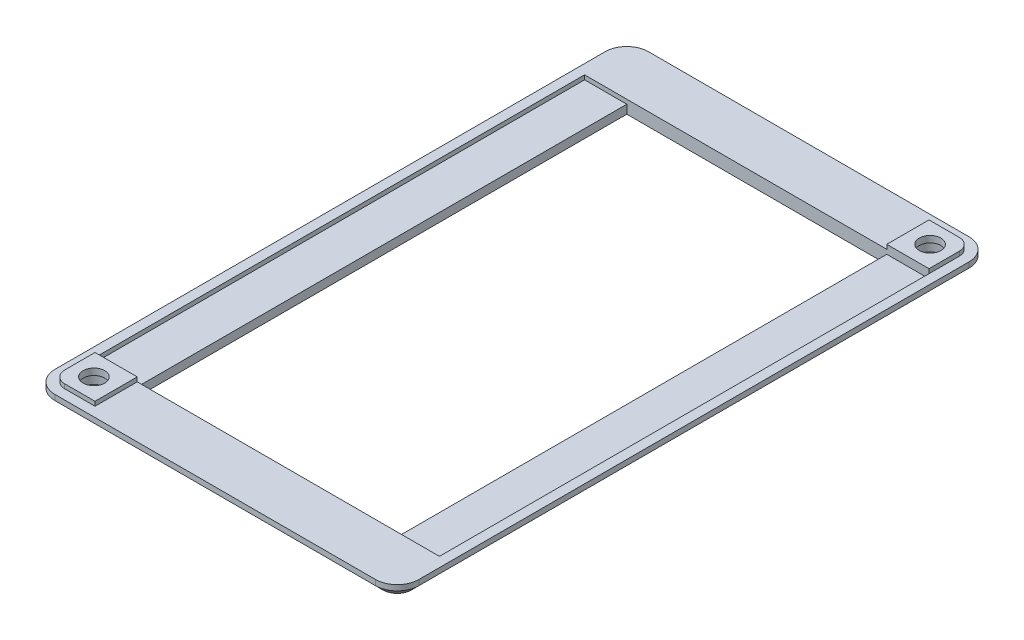
SolidWorks part; units mm, degrees
ref_plane "Front Plane" through (0, 0, 0) normal (0, 0, 1) x (1, 0, 0)
ref_plane "Top Plane" through (0, 0, 0) normal (0, 1, 0) x (1, 0, 0)
ref_plane "Right Plane" through (0, 0, 0) normal (1, 0, 0) x (0, 0, -1)
sketch "Sketch1" plane through (0, 0, 0) normal (0, 1, 0) x (1, 0, 0)
  line L1 (0, 0) -> (84, 0)
  line L2 (0, 0) -> (0, 137)
  line L3 (0, 137) -> (84, 137)
  line L4 (84, 0) -> (84, 137)
  dimension "D1" = 84
  dimension "D2" = 137
extrude "Boss-Extrude1" add sketch "Sketch1" along normal blind 3
sketch "Sketch3" plane through (0, 3, 0) normal (0, 1, 0) x (1, 0, 0)
  line L0 (81.75, 125) -> (72, 125)
  line L1 (72, 125) -> (72, 134.75)
  line L4 (12, 2.25) -> (12, 12)
  line L5 (12, 12) -> (2.25, 12)
  line L8 (2.25, 134.75) -> (2.25, 2.25)
  line L9 (2.25, 2.25) -> (81.75, 2.25)
  line L10 (81.75, 2.25) -> (81.75, 134.75)
  line L11 (81.75, 134.75) -> (2.25, 134.75)
  line L12 (2.25, 12) -> (2.25, 5)
  line L13 (5, 2.25) -> (12, 2.25)
  line L14 (81.75, 125) -> (81.75, 132)
  line L15 (79, 134.75) -> (72, 134.75)
  line L16 (0, 137) -> (0, 0)
  line L17 (0, 0) -> (84, 0)
  line L18 (84, 0) -> (84, 137)
  line L19 (84, 137) -> (0, 137)
  line L20 (0, 137) -> (0, 0) construction
  line L21 (0, 0) -> (84, 0) construction
  line L22 (84, 0) -> (84, 137) construction
  line L23 (84, 137) -> (0, 137) construction
  arc A0 (81.75, 132) -> (79, 134.75) centre (79, 132) ccw
  arc A1 (2.25, 5) -> (5, 2.25) centre (5, 5) ccw
  dimension "D2" = 2.75
  dimension "D4" = 12
  dimension "D5" = 12
  dimension "D6" = 12
  dimension "D7" = 12
  dimension "D1" = 2.25
  dimension "D3" = 0
extrude "Boss-Extrude2" add sketch "Sketch3" along normal blind 1
fillet "Fillet1" radius 5 4 edges at (84, 1.5, 0) (0, 1.5, 0) (0, 1.5, -137) (84, 1.5, -137)
sketch "Sketch4" plane through (0, 4, 0) normal (0, 1, 0) x (1, 0, 0)
  line L0 (72, 125) -> (81.75, 125) construction
  line L1 (72, 134.75) -> (72, 125) construction
  line L2 (12, 12) -> (2.25, 12) construction
  line L3 (12, 2.25) -> (12, 12) construction
  line L4 (72, 125) -> (81.75, 125) construction
  line L5 (72, 134.75) -> (72, 125) construction
  line L6 (12, 12) -> (2.25, 12) construction
  line L7 (12, 2.25) -> (12, 12) construction
  circle A0 centre (7, 7) radius 2.5
  circle A1 centre (77, 130) radius 2.5
  dimension "D1" = 5
  dimension "D4" = 5
  dimension "D2" = 5
  dimension "D3" = 5
  dimension "D5" = 5
  dimension "D6" = 5
extrude "Cut-Extrude1" cut sketch "Sketch4" against normal through all
ref_plane "Plane4" through (0, 2.5, 0) normal (0, 1, 0) x (1, 0, 0)
sketch "Sketch5" plane through (0, 2.5, 0) normal (0, 1, 0) x (1, 0, 0)
  circle A0 centre (77, 130) radius 2.5 construction
  circle A1 centre (7, 7) radius 2.5 construction
  circle A2 centre (77, 130) radius 2.5 construction
  circle A3 centre (7, 7) radius 2.5 construction
  circle A4 centre (7, 7) radius 3.5
  circle A5 centre (77, 130) radius 3.5
  dimension "D1" = 7
  dimension "D2" = 7
extrude "Cut-Extrude2" cut sketch "Sketch5" against normal through all
sketch "Sketch6" plane through (0, 3, 0) normal (0, 1, 0) x (1, 0, 0)
  line L1 (12, 12) -> (72, 12)
  line L2 (12, 12) -> (12, 125)
  line L3 (12, 125) -> (72, 125)
  line L4 (72, 12) -> (72, 125)
extrude "Cut-Extrude3" cut sketch "Sketch6" against normal through all
sketch "Sketch7" plane through (0, 3, 0) normal (0, 1, 0) x (1, 0, 0)
  line L1 (2.25, 12) -> (81.75, 12)
  line L2 (2.25, 12) -> (2.25, 125)
  line L3 (2.25, 125) -> (81.75, 125)
  line L4 (81.75, 12) -> (81.75, 125)
extrude "Cut-Extrude4" cut sketch "Sketch7" against normal blind 1
chamfer "Chamfer1" distance 1.75 angle 45 8 edges at (42, 0, -137) (1.4645, 0, -135.5355) (82.5355, 0, -135.5355) (0, 0, -68.5) (84, 0, -68.5) (1.4645, 0, -1.4645) (82.5355, 0, -1.4645) (42, 0, 0)
